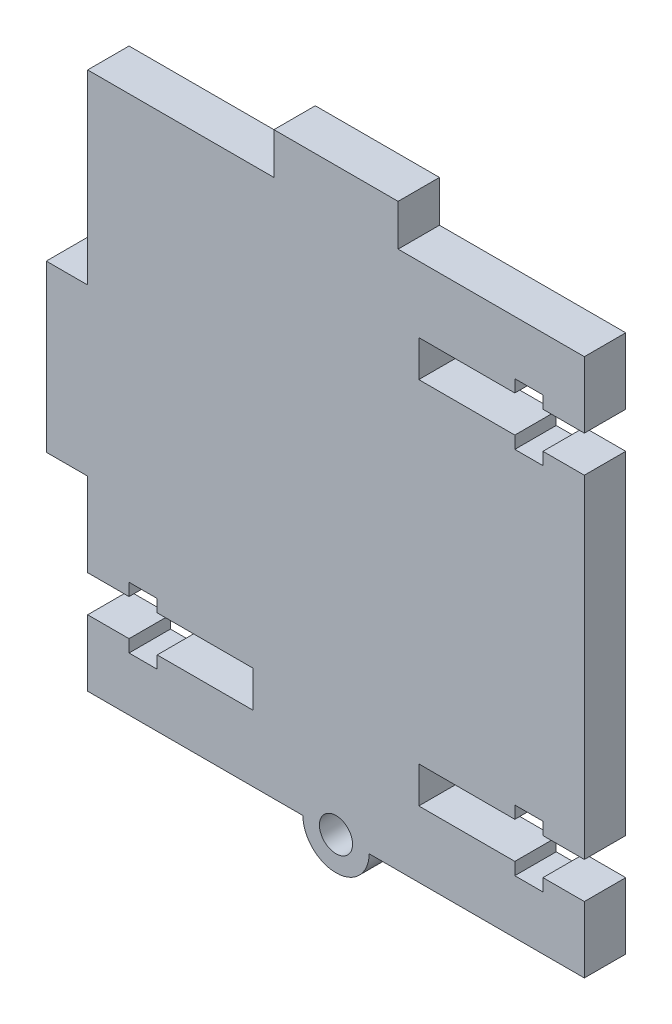
SolidWorks part; units mm, degrees
ref_plane "Front Plane" through (0, 0, 0) normal (0, 0, 1) x (1, 0, 0)
ref_plane "Top Plane" through (0, 0, 0) normal (0, 1, 0) x (1, 0, 0)
ref_plane "Right Plane" through (0, 0, 0) normal (1, 0, 0) x (0, 0, -1)
sketch "Sketch1" plane through (0, 0, 0) normal (0, 0, 1) x (1, 0, 0)
  line L0 (7.5, 32.5) -> (7.5, 37.5)
  line L1 (-30, 32.5) -> (-7.5, 32.5)
  line L2 (-30, 32.5) -> (-30, 10)
  line L3 (-30, -32.5) -> (30, -32.5)
  line L4 (30, 32.5) -> (30, -32.5)
  line L5 (7.5, 37.5) -> (-7.5, 37.5)
  line L6 (-7.5, 37.5) -> (-7.5, 32.5)
  line L7 (7.5, 32.5) -> (30, 32.5)
  line L8 (-30, -10) -> (-30, -32.5)
  line L9 (-30, 10) -> (-35, 10)
  line L11 (-30, -10) -> (-35, -10)
  line L12 (-35, 10) -> (-35, -10)
  point P13 (-32.5, 10)
  dimension "D1" = 60
  dimension "D2" = 65
  dimension "D3" = 30
  dimension "D4" = 32.5
  dimension "D5" = 15
  dimension "D6" = 22.5
  dimension "D7" = 5
  dimension "D8" = 5
  dimension "D9" = 22.5
  dimension "D10" = 20
extrude "Boss-Extrude1" add sketch "Sketch1" along normal blind 5
sketch "Sketch3" plane through (0, 0, 5) normal (0, 0, 1) x (1, 0, 0)
  line L0 (0, 0) -> (28.1265, 0) construction
  line L13 (30, -32.5) -> (30, 32.5) construction
  line L14 (30, 24.5) -> (25, 24.5)
  line L15 (25, 24.5) -> (25, 26)
  line L16 (25, 26) -> (21.6, 26)
  line L17 (21.6, 26) -> (21.6, 24.5)
  line L18 (21.6, 24.5) -> (10, 24.5)
  line L19 (10, 24.5) -> (10, 20.1)
  line L20 (10, 20.1) -> (21.6, 20.1)
  line L21 (21.6, 20.1) -> (21.6, 18.6)
  line L22 (21.6, 18.6) -> (25, 18.6)
  line L23 (25, 18.6) -> (25, 20.1)
  line L24 (25, 20.1) -> (30, 20.1)
  line L25 (30, 24.5) -> (30, 20.1)
  line L26 (-7.5, 32.5) -> (-30, 32.5) construction
  line L27 (0, 0) -> (0, 42.4523) construction
  line L28 (30, -24.5) -> (30, -20.1)
  line L29 (25, -20.1) -> (30, -20.1)
  line L30 (25, -18.6) -> (25, -20.1)
  line L31 (21.6, -18.6) -> (25, -18.6)
  line L32 (21.6, -20.1) -> (21.6, -18.6)
  line L33 (10, -20.1) -> (21.6, -20.1)
  line L34 (10, -24.5) -> (10, -20.1)
  line L35 (21.6, -24.5) -> (10, -24.5)
  line L36 (21.6, -26) -> (21.6, -24.5)
  line L37 (25, -26) -> (21.6, -26)
  line L38 (25, -24.5) -> (25, -26)
  line L39 (30, -24.5) -> (25, -24.5)
  line L40 (-30, -24.5) -> (-25, -24.5)
  line L41 (-25, -24.5) -> (-25, -26)
  line L42 (-25, -26) -> (-21.6, -26)
  line L43 (-21.6, -26) -> (-21.6, -24.5)
  line L44 (-21.6, -24.5) -> (-10, -24.5)
  line L45 (-10, -24.5) -> (-10, -20.1)
  line L46 (-10, -20.1) -> (-21.6, -20.1)
  line L47 (-21.6, -20.1) -> (-21.6, -18.6)
  line L48 (-21.6, -18.6) -> (-25, -18.6)
  line L49 (-25, -18.6) -> (-25, -20.1)
  line L50 (-25, -20.1) -> (-30, -20.1)
  line L51 (-30, -24.5) -> (-30, -20.1)
  dimension "D8" = 4.4
  dimension "D9" = 1.5
  dimension "D10" = 1.5
  dimension "D11" = 3.4
  dimension "D12" = 5
  dimension "D13" = 8
  dimension "D14" = 20
extrude "Cut-Extrude1" cut sketch "Sketch3" against normal blind 5
sketch "Sketch10" plane through (0, 0, 5) normal (0, 0, 1) x (1, 0, 0)
  line L0 (0, 0) -> (0, -37.4843) construction
  line L1 (-30, -32.5) -> (30, -32.5) construction
  circle A0 centre (0, -32.5) radius 2
  circle A1 centre (0, -32.5) radius 4
  dimension "D1" = 4
  dimension "D2" = 8
extrude "Boss-Extrude3" add sketch "Sketch10" against normal blind 5
sketch "Sketch11" plane through (0, 0, 5) normal (0, 0, 1) x (1, 0, 0)
  line L0 (-2, -32.5) -> (2, -32.5) construction
  circle A0 centre (0, -32.5) radius 2
extrude "Cut-Extrude3" cut sketch "Sketch11" against normal blind 5
